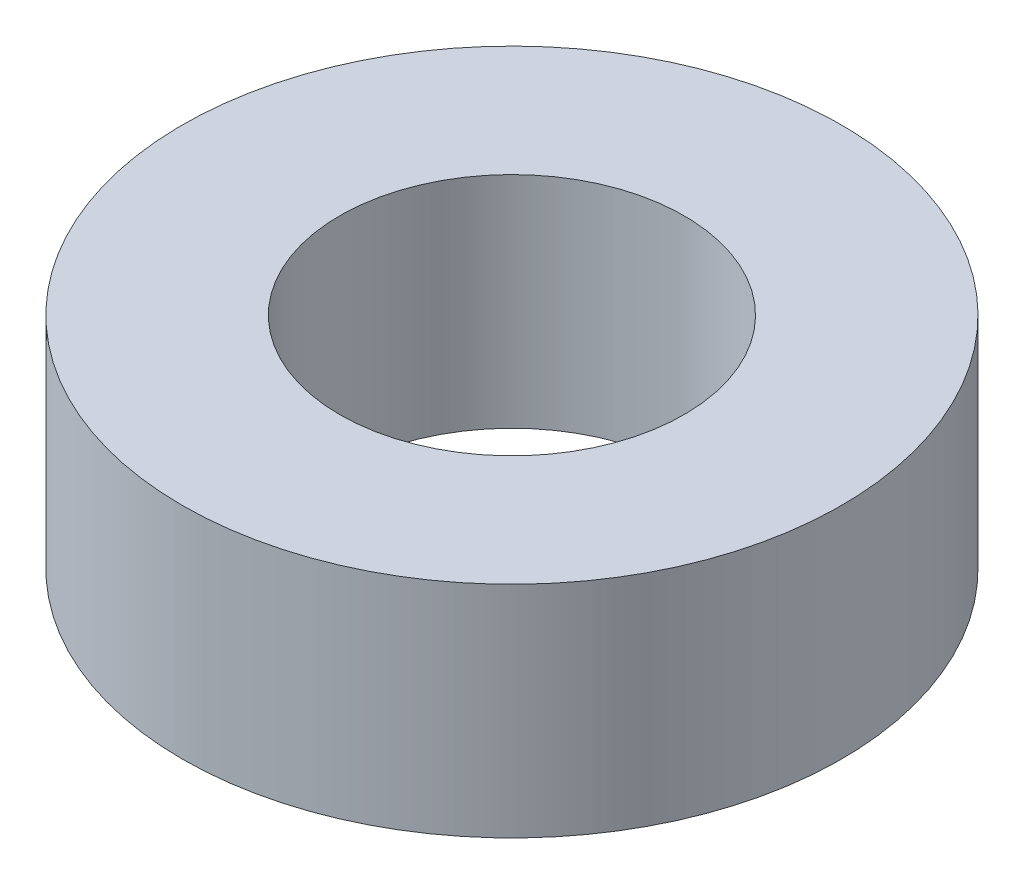
SolidWorks part; units mm, degrees
material "6061 Alloy"
ref_plane "Front Plane" through (0, 0, 0) normal (0, 0, 1) x (1, 0, 0)
ref_plane "Top Plane" through (0, 0, 0) normal (0, 1, 0) x (1, 0, 0)
ref_plane "Right Plane" through (0, 0, 0) normal (1, 0, 0) x (0, 0, -1)
sketch "Sketch1" plane through (0, 0, 0) normal (0, 1, 0) x (1, 0, 0)
  circle A0 centre (0, 0) radius 2.4892
  circle A1 centre (0, 0) radius 4.7625
  dimension "D1" = 4.9784
  dimension "D2" = 9.525
extrude "Boss-Extrude1" add sketch "Sketch1" along normal blind 3.175
